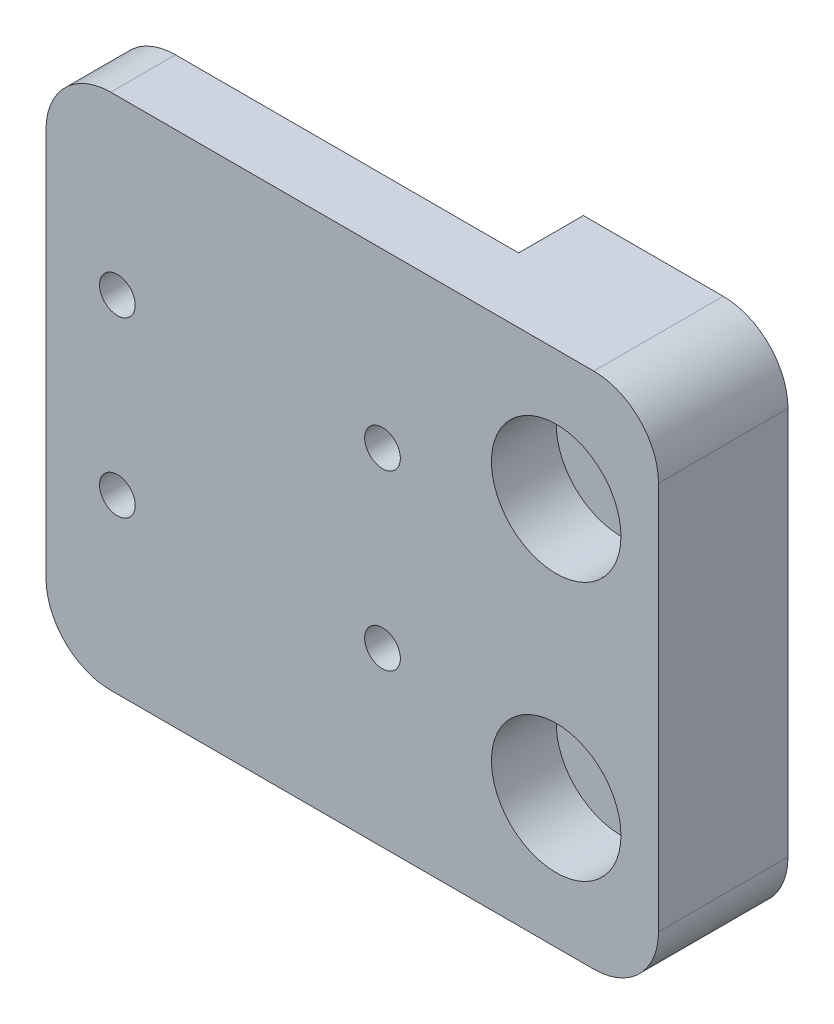
SolidWorks part; units mm, degrees
ref_plane "Front Plane" through (0, 0, 0) normal (0, 0, 1) x (1, 0, 0)
ref_plane "Top Plane" through (0, 0, 0) normal (0, 1, 0) x (1, 0, 0)
ref_plane "Right Plane" through (0, 0, 0) normal (1, 0, 0) x (0, 0, -1)
sketch "Sketch1" plane through (0, 0, 0) normal (0, 0, 1) x (1, 0, 0)
  line L1 (-10.033, -25.4) -> (10.033, -25.4)
  line L2 (-10.033, -25.4) -> (-10.033, 25.4)
  line L3 (-10.033, 25.4) -> (10.033, 25.4)
  line L4 (10.033, -25.4) -> (10.033, 25.4)
  line L5 (-10.033, -25.4) -> (10.033, 25.4) construction
  line L6 (-10.033, 25.4) -> (10.033, -25.4) construction
  point P0 (0, 0)
  dimension "D1" = 20.066
  dimension "D2" = 50.8
extrude "Boss-Extrude1" add sketch "Sketch1" along normal blind 12.7
sketch "Sketch2" plane through (0, 0, 12.7) normal (0, 0, 1) x (1, 0, 0)
  line L0 (0, 25.4) -> (0, -25.4) construction
  line L1 (10.033, 25.4) -> (-10.033, 25.4) construction
  line L2 (-10.033, -25.4) -> (10.033, -25.4) construction
  circle A0 centre (0, 12.7) radius 2.286
  circle A1 centre (0, -12.7) radius 2.286
  point P10 (0, 0)
  dimension "D1" = 4.572
  dimension "D2" = 12.7
  dimension "D3" = 12.7
extrude "Cut-Extrude1" cut sketch "Sketch2" against normal through all
sketch "Sketch3" plane through (0, 0, 12.7) normal (0, 0, 1) x (1, 0, 0)
  line L0 (-10.033, -25.4) -> (10.033, -25.4) construction
  line L1 (-10.033, 25.4) -> (-50.033, 25.4)
  line L2 (-10.033, 25.4) -> (-10.033, -25.4)
  line L3 (-10.033, -25.4) -> (-50.033, -25.4)
  line L4 (-50.033, 25.4) -> (-50.033, -25.4)
  dimension "D1" = 40
extrude "Boss-Extrude2" add sketch "Sketch3" against normal blind 6.35
sketch "Sketch5" plane through (0, 0, 6.35) normal (0, 0, -1) x (-1, 0, 0)
  line L0 (50.033, 0) -> (10.033, 0) construction
  line L1 (50.033, 25.4) -> (50.033, -25.4) construction
  line L2 (10.033, -25.4) -> (10.033, 25.4) construction
  line L4 (17.033, -8.5) -> (43.033, -8.5) construction
  line L5 (17.033, -8.5) -> (17.033, 8.5) construction
  line L6 (17.033, 8.5) -> (43.033, 8.5) construction
  line L7 (43.033, -8.5) -> (43.033, 8.5) construction
  line L8 (17.033, -8.5) -> (43.033, 8.5) construction
  line L9 (17.033, 8.5) -> (43.033, -8.5) construction
  circle A0 centre (43.033, 8.5) radius 1.75
  circle A1 centre (17.033, 8.5) radius 1.75
  circle A2 centre (43.033, -8.5) radius 1.75
  circle A3 centre (17.033, -8.5) radius 1.75
  point P6 (30.033, 0)
  dimension "D3" = 3.5
  dimension "D1" = 26
  dimension "D2" = 17
extrude "Cut-Extrude2" cut sketch "Sketch5" against normal through all
sketch "Sketch6" plane through (0, 0, 12.7) normal (0, 0, 1) x (1, 0, 0)
  circle A0 centre (0, 12.7) radius 6.35
  circle A1 centre (0, -12.7) radius 6.35
  dimension "D1" = 12.7
extrude "Cut-Extrude3" cut sketch "Sketch6" against normal blind 6.35
fillet "Fillet1" radius 6.35 4 edges at (10.033, 25.4, 6.35) (-50.033, 25.4, 9.525) (-50.033, -25.4, 9.525) (10.033, -25.4, 6.35)
